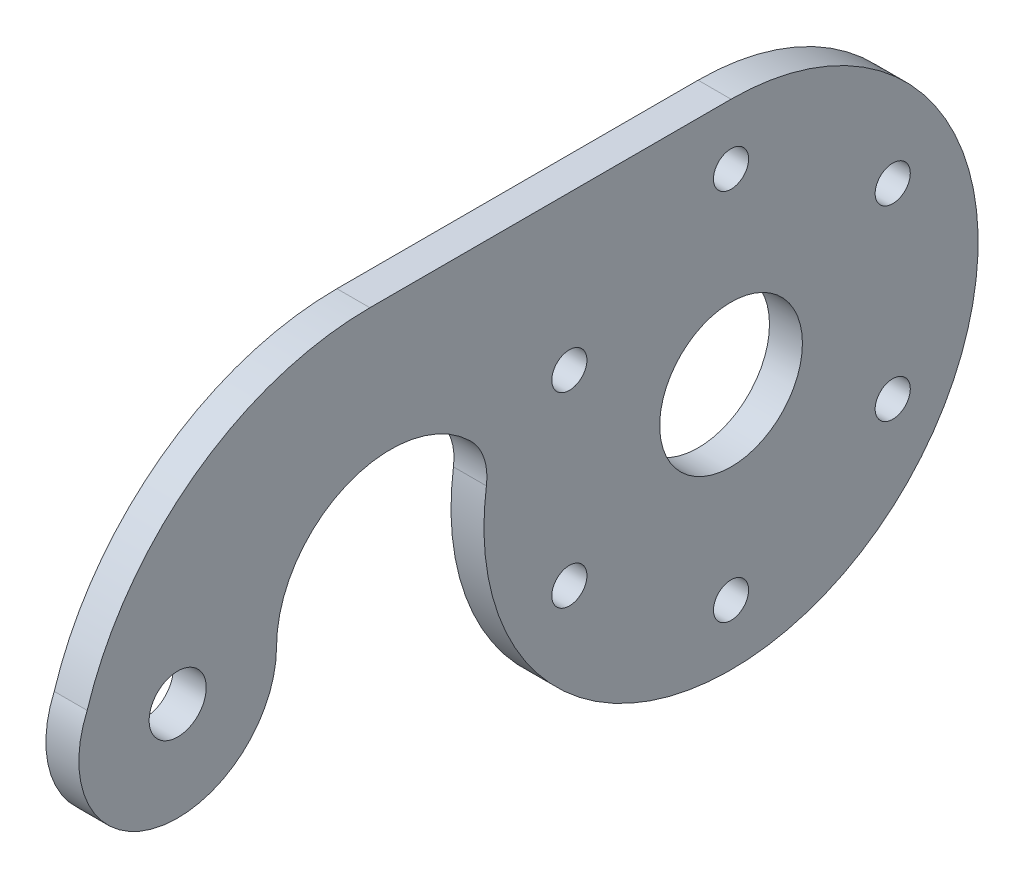
SolidWorks part; units mm, degrees
ref_plane "Front Plane" through (0, 0, 0) normal (0, 0, 1) x (1, 0, 0)
ref_plane "Top Plane" through (0, 0, 0) normal (0, 1, 0) x (1, 0, 0)
ref_plane "Right Plane" through (0, 0, 0) normal (1, 0, 0) x (0, 0, -1)
sketch "Sketch1" plane through (0, 0, 0) normal (1, 0, 0) x (0, 0, -1)
  line L0 (0, 0) -> (-70.5057, 0) construction
  line L1 (0, 22.5) -> (-32.8866, 22.5)
  circle A0 centre (0, 0) radius 22.5
  circle A1 centre (-50.3866, 0) radius 9
  circle A2 centre (-31, 0) radius 8.5
  circle A3 centre (-31, 0) radius 10.3866
  arc A4 (-58.6291, 3.6141) -> (-32.8866, 22.5) centre (-32.8866, -4.4871) cw
  dimension "D1" = 31
  dimension "D2" = 18
  dimension "D3" = 45
  dimension "D4" = 17.5
extrude "Boss-Extrude1" add sketch "Sketch1" along normal blind 3
fillet "Fillet2" radius 5 1 edges at (1.5, 5.0529, 21.9253)
sketch "Sketch2" plane through (3, 0, 0) normal (1, 0, 0) x (0, 0, -1)
  line L0 (0, 0) -> (-13.5676, -10.1733) construction
  line L1 (0, 0) -> (0, 18.7492) construction
  circle A0 centre (0, 0) radius 6.5
  circle A1 centre (-50.3866, 0) radius 2.6
  circle A2 centre (0, 17) radius 1.6
  circle A3 centre (14.7224, 8.5) radius 1.6
  circle A4 centre (14.7224, -8.5) radius 1.6
  circle A5 centre (0, -17) radius 1.6
  circle A6 centre (-14.7224, -8.5) radius 1.6
  circle A7 centre (-14.7224, 8.5) radius 1.6
  point P22 (0, 0)
  dimension "D1" = 5.2
  dimension "D2" = 13
  dimension "D3" = 3.2
  dimension "D4" = 17
  dimension "D5" = 6
extrude "Cut-Extrude1" cut sketch "Sketch2" against normal through all
